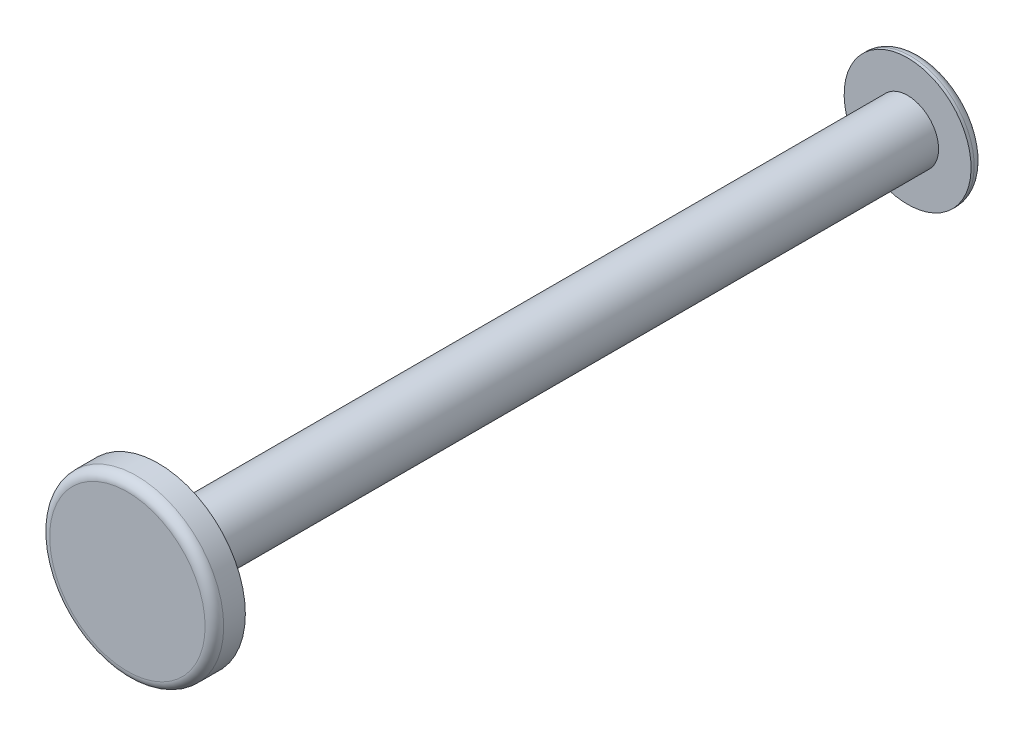
SolidWorks part; units mm, degrees
ref_plane "Plane1" through (0, 0, 0) normal (0, 0, 1) x (1, 0, 0)
ref_plane "Plane2" through (0, 0, 0) normal (0, 1, 0) x (1, 0, 0)
ref_plane "Plane3" through (0, 0, 0) normal (1, 0, 0) x (0, 0, -1)
other "Configuration Table"
sketch "Sketch1" plane through (0, 0, 0) normal (0, 0, 1) x (1, 0, 0)
  circle A0 centre (0, 17.5) radius 1 construction
  circle A1 centre (0, 17.5) radius 1
extrude "Base-Extrude" add sketch "Sketch1" against normal up to surface (24.2 mm away)
sketch "Sketch2" plane through (0, 0, 0) normal (0, 0, 1) x (1, 0, 0)
  circle A0 centre (0, 17.5) radius 2.81
  circle A1 centre (0, 17.5) radius 1 construction
  dimension "D1" = 5.62
extrude "Boss-Extrude1" add sketch "Sketch2" along normal blind 1
fillet "Fillet1" radius 0.3 1 edges at (2.81, 17.5, 1)
sketch "Sketch3" plane through (0, 0, -24.2) normal (0, 0, -1) x (-1, 0, 0)
  circle A0 centre (0, 17.5) radius 2.05
  dimension "D1" = 4.1
extrude "Boss-Extrude2" add sketch "Sketch3" along normal blind 0.4
sketch "Sketch4" plane through (0, 0, -24.6) normal (0, 0, -1) x (-1, 0, 0)
  line L0 (-0.9184, 17.8957) -> (0.9184, 17.1043) construction
  line L1 (0.9184, 17.1043) -> (-0.9184, 17.8957)
  arc A0 (-0.9184, 17.8957) -> (0.9184, 17.1043) centre (0, 17.5) ccw
  dimension "D1" = 2
revolve "Cut-Revolve1" cut sketch "Sketch4" angle 360 about L0
fillet "Fillet2" radius 0.3 1 edges at (0, 19.55, -24.6)
